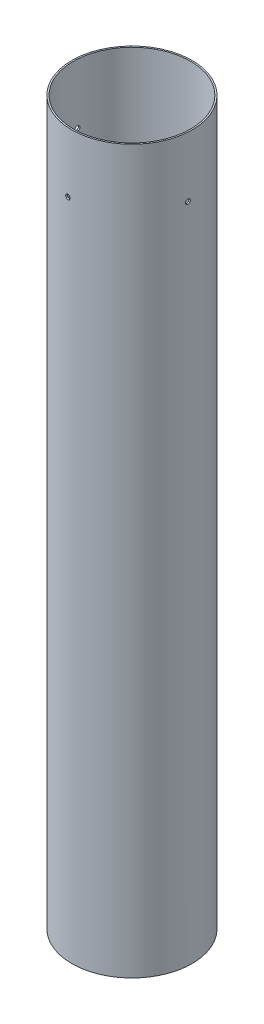
SolidWorks part; units mm, degrees
material "Wildman Fiberglass"
ref_plane "Front Plane" through (0, 0, 0) normal (0, 0, 1) x (1, 0, 0)
ref_plane "Top Plane" through (0, 0, 0) normal (0, 1, 0) x (1, 0, 0)
ref_plane "Right Plane" through (0, 0, 0) normal (1, 0, 0) x (0, 0, -1)
sketch "Sketch1" plane through (0, 0, 0) normal (0, 1, 0) x (1, 0, 0)
  circle A0 centre (0, 0) radius 49.53
  circle A1 centre (0, 0) radius 50.8
  dimension "D1" = 101.6
  dimension "D2" = 99.06
extrude "Boss-Extrude1" add sketch "Sketch1" along normal blind 609.6
extrude "Cut-Extrude1" cut sketch "Sketch2" against normal blind 12.7
sketch "Sketch2" plane through (122.9, 815.5954, -42.5514) normal (0.0679, 0, -0.9977) x (-0.9977, 0, -0.0679)
  circle A0 centre (119.7263, -256.7954) radius 1.9844
  point P2 (0, 0)
  point P3 (0, 0)
  point P6 (0, 0)
pattern_circular "CirPattern1" count 4 over 360 of "Cut-Extrude1"
equation "\"Length\"=24"
equation "\"D1@Boss-Extrude1\"=\"Length\""
